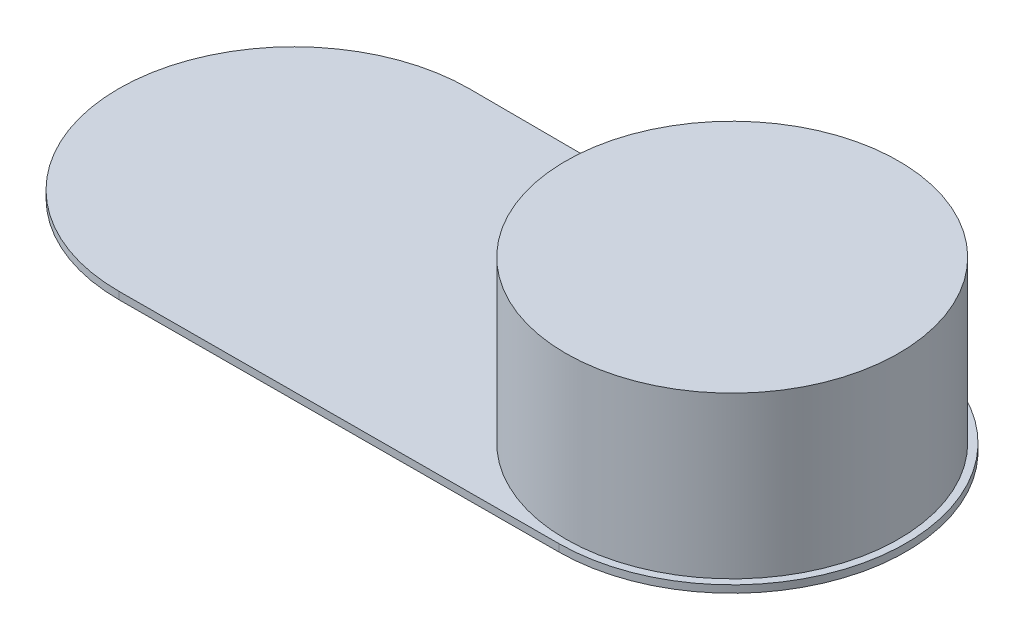
SolidWorks part; units mm, degrees
ref_plane "Front Plane" through (0, 0, 0) normal (0, 0, 1) x (1, 0, 0)
ref_plane "Top Plane" through (0, 0, 0) normal (0, 1, 0) x (1, 0, 0)
ref_plane "Right Plane" through (0, 0, 0) normal (1, 0, 0) x (0, 0, -1)
sketch "Sketch1" plane through (0, 0, 0) normal (0, 1, 0) x (1, 0, 0)
  line L0 (-300, 0) -> (0, 0) construction
  line L1 (-299.6167, 114.9994) -> (0.38, 113.9994)
  line L2 (-299.6, 119.9993) -> (0.3967, 118.9993)
  line L3 (0.38, -113.9994) -> (-299.6167, -114.9994)
  line L4 (0.3967, -118.9993) -> (-299.6, -119.9993)
  circle A0 centre (-300, 0) radius 110 construction
  circle A1 centre (0, 0) radius 109 construction
  arc A2 (-299.6167, 114.9994) -> (-299.6167, -114.9994) centre (-300, 0) ccw
  arc A3 (0.38, -113.9994) -> (0.38, 113.9994) centre (0, 0) ccw
  circle A4 centre (-300, 0) radius 115 construction
  circle A5 centre (0, 0) radius 114 construction
  circle A6 centre (0, 0) radius 109
  arc A7 (0.3967, -118.9993) -> (0.3967, 118.9993) centre (0, 0) ccw
  arc A8 (-299.6, 119.9993) -> (-299.6, -119.9993) centre (-300, 0) ccw
  dimension "D2" = 218
  dimension "D3" = 220
  dimension "D1" = 300
  dimension "D4" = 5
  dimension "D5" = 5
extrude "Boss-Extrude1" add sketch "Sketch1" along normal blind 5 contours L3 A3 L1 A2 A6 | L2 A8 L4 A7 A3 L3 A2 L1
sketch "Sketch2" plane through (0, 5, 0) normal (0, 1, 0) x (1, 0, 0)
  circle A0 centre (0, 0) radius 109 construction
  circle A1 centre (0, 0) radius 109
  circle A2 centre (0, 0) radius 114
  dimension "D1" = 5
extrude "Boss-Extrude2" add sketch "Sketch2" along normal blind 105.1
sketch "Sketch3" plane through (0, 110.1, 0) normal (0, 1, 0) x (1, 0, 0)
  circle A0 centre (0, 0) radius 114 construction
  circle A1 centre (0, 0) radius 114
extrude "Boss-Extrude3" add sketch "Sketch3" along normal blind 5
